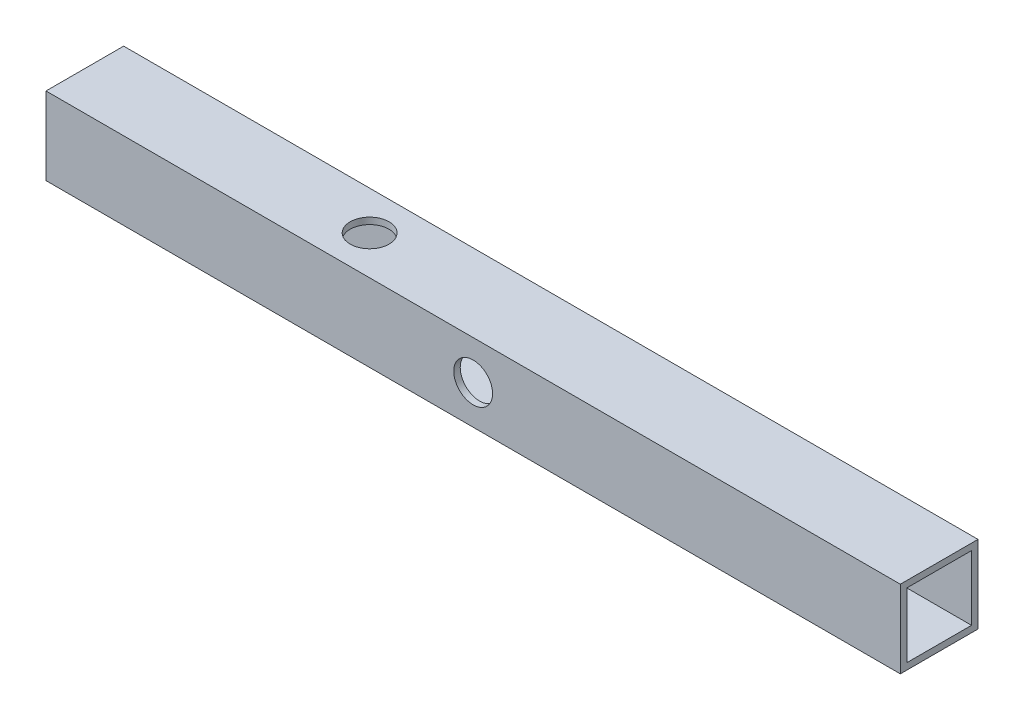
SolidWorks part; units mm, degrees
ref_plane "Front Plane" through (0, 0, 0) normal (0, 0, 1) x (1, 0, 0)
ref_plane "Top Plane" through (0, 0, 0) normal (0, 1, 0) x (1, 0, 0)
ref_plane "Right Plane" through (0, 0, 0) normal (1, 0, 0) x (0, 0, -1)
sketch "Sketch1" plane through (0, 0, 0) normal (1, 0, 0) x (0, -1, 0)
  line L1 (-9.525, 9.525) -> (9.525, 9.525)
  line L2 (-9.525, 9.525) -> (-9.525, -9.525)
  line L3 (-9.525, -9.525) -> (9.525, -9.525)
  line L4 (9.525, 9.525) -> (9.525, -9.525)
  line L5 (-9.525, 9.525) -> (9.525, -9.525) construction
  line L6 (-9.525, -9.525) -> (9.525, 9.525) construction
  line L7 (-7.9375, 7.9375) -> (7.9375, 7.9375)
  line L8 (-7.9375, 7.9375) -> (-7.9375, -7.9375)
  line L9 (-7.9375, -7.9375) -> (7.9375, -7.9375)
  line L10 (7.9375, 7.9375) -> (7.9375, -7.9375)
  line L11 (-7.9375, 7.9375) -> (7.9375, -7.9375) construction
  line L12 (-7.9375, -7.9375) -> (7.9375, 7.9375) construction
  point P0 (0, 0)
  point P5 (0, 0)
  dimension "D1" = 15.875
  dimension "D2" = 19.05
extrude "Boss-Extrude1" add sketch "Sketch1" along normal mid plane 209.55
sketch "Sketch4" plane through (0, 0, -9.525) normal (0, 0, 1) x (1, 0, 0)
  line L2 (-69.85, 0) -> (69.85, 0) construction
  line L4 (69.85, 0) -> (114.3, 0) construction
  line L6 (104.775, -9.525) -> (104.775, 9.525) construction
  circle A0 centre (-69.85, 0) radius 4.7625
  circle A1 centre (69.85, 0) radius 4.7625
  dimension "D2" = 9.525
  dimension "D1" = 139.7
  dimension "D4" = 9.525
  dimension "D3" = 34.925
extrude "PowerSupply Mount Holes" cut sketch "Sketch4" along normal up to next
sketch "Sketch5" plane through (0, 0, 9.525) normal (0, 0, 1) x (1, 0, 0)
  circle A0 centre (0, 0) radius 4.7625
  dimension "D1" = 9.525
extrude "Cut-Extrude1" cut sketch "Sketch5" against normal up to next
sketch "Sketch6" plane through (0, 9.525, 0) normal (0, -1, 0) x (1, 0, 0)
  line L1 (-104.775, -9.525) -> (-104.775, 9.525) construction
  circle A0 centre (-34.925, 0) radius 4.7625
  point P6 (-104.775, 0)
  dimension "D1" = 9.525
  dimension "D2" = 69.85
extrude "Cut-Extrude2" cut sketch "Sketch6" along normal through all
equation "\"Height\"= 32in"
equation "\"Width\"= 23in"
equation "\"Depth\"= 20in"
equation "\"Plexi\"= .121in"
equation "\"MagnetThickness\"= 0.125in"
equation "\"MagnetDiameter\"= 12mm"
equation "\"DoorPlexi\" = \"Plexi\""
equation "\"BasePlateThickness\" = 0.5in"
equation "\"BasePlateWidth\" = \"Width\"+\"EBWidth\"-2*\"Plexi\""
equation "\"BasePlateDepth\" = \"TopBarDepth\"+2*\"CornerCube\""
equation "\"Boxsize\" = .75in"
equation "\"BoxsizeHalf\" = \"Boxsize\"/2"
equation "\"Boxinner\" = .625in"
equation "\"CornerCube\" = 0.75in"
equation "\"FingerLength\" = 1.125in"
equation "\"FingerWidth\" = .625in"
equation "\"Cutwidth\"= .016in"
equation "\"Earsize\"= 1in + \"Cutwidth\" /2"
equation "\"Slotsize\" = 1in - \"CutWidth\" / 2"
equation "\"InnerWidth\" = \"Width\" - 2* \"Plexi\""
equation "\"InnerHeight\" = \"Height\" -2 * \"Plexi\""
equation "\"InnerDepth\" = \"Depth\" - 2*\"Plexi\""
equation "\"RearNumHoles\" = 4"
equation "\"RearHolesBorder\" = 2.25"
equation "\"RearHoleSpacing\" = (\"Width\" - 2*\"RearHolesBorder\") / (\"RearNumHoles\"-1)"
equation "\"RearBarLength\" = (\"InnerWidth\"-2*\"CornerCube\")"
equation "\"RearTopNumHoles\" = 4"
equation "\"RearTopHolesBorder\" = 3.1"
equation "\"RearTopHolesSpacing\" = (\"Width\" - 2*\"RearTopHolesBorder\") / (\"RearTopNumHoles\"-1)"
equation "\"SideTopNumHoles\" = 4"
equation "\"SideTopHoleOffset\"=\"CornerCube\"+\"FingerLength\"+\"Plexi\"+.5"
equation "\"SideHorizNumHoles\" = 4"
equation "\"SideHorizHoleBorder\" = 1.50"
equation "\"SideVertBarLength\"=\"Height\"-\"BasePlateThickness\"-2*\"CornerCube\"-\"Plexi\""
equation "\"SideVertNumHoles\" = 4"
equation "\"SideVertHolesBorder\" = \"CornerCube\"+\"FingerLength\"+1.50"
equation "\"SideVertHoleSpacing\" = (\"InnerHeight\" - 2*\"SideVertHolesBorder\") / (\"SideVertNumHoles\"-1)"
equation "\"RearSideVertNumHoles\" = 4"
equation "\"RearSideVertHolesBorder\" = 2.4"
equation "\"RearSideVertHoleSpacing\" = (\"InnerHeight\" - 2*\"RearSideVertHolesBorder\") / (\"RearSideVertNumHoles\"-1)"
equation "\"RivetDia\" = .228in"
equation "\"SlotDepth\" = \"Plexi\" + 0.75in + .005in"
equation "\"SideSlotWidth\"   = \"Plexi\"+.005in"
equation "\"SidePanelVertSpacing\" = (\"Height\"-2*(1.75-\"Plexi\")) / 5"
equation "\"BottomPanelSideHoleSpacing\" = (\"InnerDepth\"-2*(1.75-\"Plexi\")) / 4"
equation "\"FrontDoorGap\" = .1in"
equation "\"TopDepth\" = \"Depth\"-\"DoorPlexi\"-\"FrontDoorGap\""
equation "\"TopBarDepth\" = \"Depth\"-\"DoorPlexi\"-\"Plexi\"-2*\"MagnetThickness\"-2*\"CornerCube\""
equation "\"CoolerDepth\" = 12in"
equation "\"ShelfDepth\" = \"TopBarDepth\"+\"CornerCube\"-\"CoolerDepth\""
equation "\"ShelfBarWidth\" = \"EBWidth\"-\"Boxsize\""
equation "\"ShelfGap\" = 0.5in"
equation "\"ShelfBarWidthShort\" = \"ShelfBarWidth\"-\"Boxsize\"-\"ShelfGap\""
equation "\"IntakeWidth\"=4in"
equation "\"IntakeHeight\"=2in"
equation "\"ExhaustWidth\"=4in"
equation "\"ExhaustHeight\"=2in"
equation "\"VentSpacing\"=7in"
equation "\"AngleBracketLength\"=20mm"
equation "\"AngleBracketWidth\"=.5in"
equation "\"AngleBracketThickness\"=.125in"
equation "\"AngleBracketHolePos\"=15mm"
equation "\"AngleBracketHoleDia\"=\"Rivet3_16Dia\""
equation "\"ShelfBarAngleHole\"=\"ShelfGap\"+\"Boxsize\"+\"AngleBracketHolePosShort\""
equation "\"D1@Boss-Extrude1\"=\"ShelfBarWidth\""
equation "\"SideTopHoleSpacing\" = (\"TopBarDepth\"-2*\"SideTopHoleOffset\") / (\"SideTopNumHoles\"-1)"
equation "\"SideHorizHoleSpacing\" = (\"TopBarDepth\"-2*\"SideHorizHoleBorder\") / (\"SideHorizNumHoles\"-1)"
equation "\"EBWidth\" = 9in"
equation "\"ShelfBarDepth\"=\"ShelfDepth\"-2*\"CornerCube\""
equation "\"ShelfWidth\" = \"EBWidth\"-\"ShelfGap\""
equation "\"D4@Sketch4\"=\"BoxsizeHalf\""
equation "\"ComponentMountDia\"=0.1770"
equation "\"ShelfThickness\" = .1250in"
equation "\"Rivet3_16Dia\" = .191in"
equation "\"BinderPostDia\" = .228in"
equation "\"ShelfHeight1\" = 13in"
equation "\"ShelfHeight2\" = 24in"
equation "\"VentVertLocation\"=12.75in"
equation "\"PSBracketThickness\" = .0641in"
equation "\"EBForwardMountOffset\" = 4.0in"
equation "\"EBForwardMount\" = 2*\"Boxsize\"+\"CoolerDepth\"+\"EBForwardMountOffset\""
equation "\"EBRearwardMountOffset\" = 1.5in"
equation "\"EBRearwardMount\"= \"Boxsize\"+\"EBRearwardMountOffset\""
equation "\"AngleBracketLengthShort\"=.625in"
equation "\"AngleBracketLengthLong\"=1in"
equation "\"AngleBracketHolePosShort\"=.358in"
equation "\"AngleBracketHolePosLong\"=.7in"
equation "\"MagSealWidth\" = \"InnerWidth\""
equation "\"MagSealHeight\" = \"Height\"-\"BasePlateThickness\"-\"Plexi\""
equation "\"MagWidth\" = .500in"
equation "\"SiliconeSealOD\" = .3125in"
equation "\"SiliconeSealID\" = .1875in"
equation "\"SiliconeSealWidth\" = \"MagSealWidth\" - 2*\"MagWidth\"-\"SiliconeSealOD\""
equation "\"SiliconeSealHeigth\" = \"MagSealHeight\" - 2*\"MagWidth\"-\"SiliconeSealOD\""
equation "\"HooknLoopThick\" = .085in"
equation "\"HooknLoopWidth\" = 0.75in"
equation "\"HooknLoopHeigth\" = 0.75in"
equation "\"RivNutHeight\" = 0.015in"
equation "\"D3@Sketch4\"=(\"ShelfBarWidth\"-5.5)/2"
equation "\"D2@Sketch6\"=\"ShelfBarWidth\"/3"
